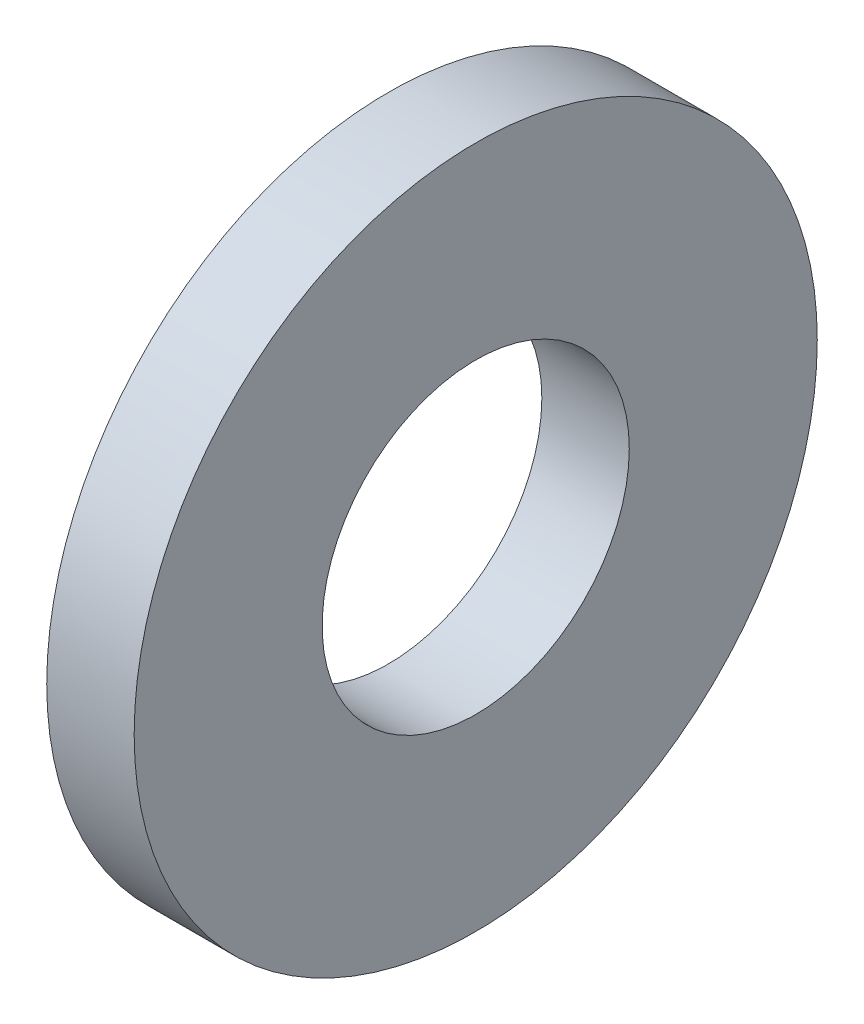
SolidWorks part; units mm, degrees
ref_plane "Front Plane" through (0, 0, 0) normal (0, 0, 1) x (1, 0, 0)
ref_plane "Top Plane" through (0, 0, 0) normal (0, 1, 0) x (1, 0, 0)
ref_plane "Right Plane" through (0, 0, 0) normal (1, 0, 0) x (0, 0, -1)
sketch "Sketch1" plane through (0, 0, 0) normal (1, 0, 0) x (0, 0, -1)
  circle A0 centre (0, 0) radius 7.9375
  circle A1 centre (0, 0) radius 3.5687
  dimension "OD" = 15.875
  dimension "ID" = 7.1374
extrude "Boss-Extrude1" add sketch "Sketch1" along normal blind 2.032
